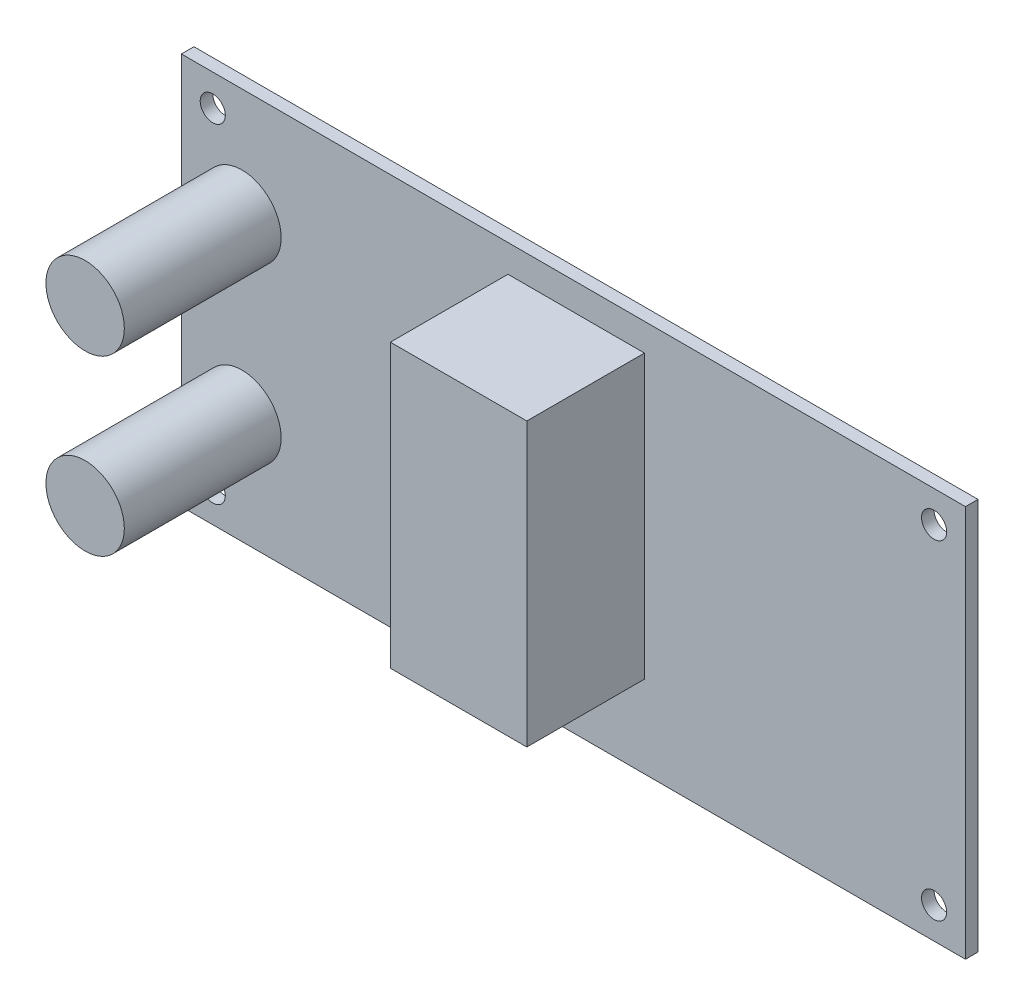
SolidWorks part; units mm, degrees
ref_plane "Plan de face" through (0, 0, 0) normal (0, 0, 1) x (1, 0, 0)
ref_plane "Plan de dessus" through (0, 0, 0) normal (0, 1, 0) x (1, 0, 0)
ref_plane "Plan de droite" through (0, 0, 0) normal (1, 0, 0) x (0, 0, -1)
sketch "Esquisse1" plane through (0, 0, 0) normal (0, 0, 1) x (1, 0, 0)
  line L0 (-46, 21) -> (46, -21) construction
  line L1 (-50, 25) -> (50, 25)
  line L2 (-50, 25) -> (-50, -25)
  line L3 (-50, -25) -> (50, -25)
  line L4 (50, 25) -> (50, -25)
  circle A0 centre (-46, 21) radius 1.6
  circle A1 centre (46, 21) radius 1.6
  circle A2 centre (46, -21) radius 1.6
  circle A3 centre (-46, -21) radius 1.6
  point P12 (0, 0)
  point P13 (0, -25)
  point P14 (-50, 0)
  dimension "D3" = 3.2
  dimension "D1" = 100
  dimension "D2" = 50
  dimension "D4" = 92
  dimension "D5" = 42
extrude "Boss.-Extru.1" add sketch "Esquisse1" along normal blind 1.6
sketch "Esquisse2" plane through (0, 0, 1.6) normal (0, 0, 1) x (1, 0, 0)
  line L0 (-42.278, 11.0526) -> (-42.278, -11.0526) construction
  line L1 (-50, 25) -> (-50, -25) construction
  circle A0 centre (-42.278, 11.0526) radius 5
  circle A1 centre (-42.278, -11.0526) radius 5
  point P4 (-42.278, 0)
  point P7 (-50, 0)
  dimension "D1" = 10
extrude "Boss.-Extru.2" add sketch "Esquisse2" along normal blind 20
sketch "Esquisse3" plane through (0, 0, 1.6) normal (0, 0, 1) x (1, 0, 0)
  line L1 (-8.3462, 21.491) -> (9.0566, 21.491)
  line L2 (-8.3462, 21.491) -> (-8.3462, -14.5276)
  line L3 (-8.3462, -14.5276) -> (9.0566, -14.5276)
  line L4 (9.0566, 21.491) -> (9.0566, -14.5276)
extrude "Boss.-Extru.3" add sketch "Esquisse3" along normal blind 15
